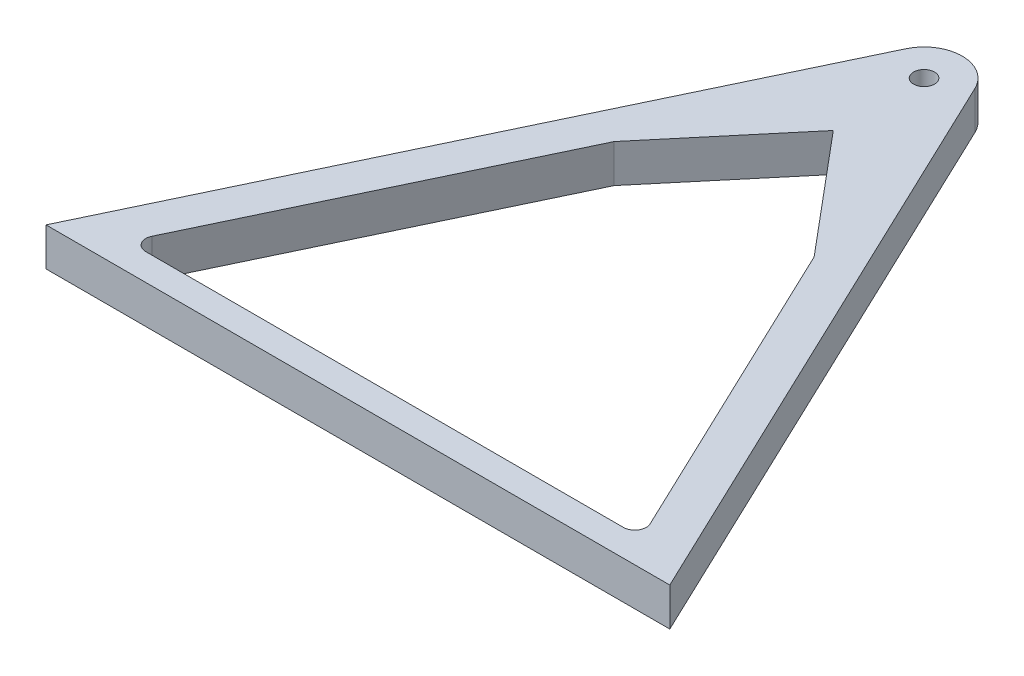
SolidWorks part; units mm, degrees
ref_plane "Front Plane" through (0, 0, 0) normal (0, 0, 1) x (1, 0, 0)
ref_plane "Top Plane" through (0, 0, 0) normal (0, 1, 0) x (1, 0, 0)
ref_plane "Right Plane" through (0, 0, 0) normal (1, 0, 0) x (0, 0, -1)
sketch "Sketch1" plane through (0, 0, 0) normal (0, 1, 0) x (1, 0, 0)
  line L0 (76.2, 0) -> (-76.2, 0) construction
  line L1 (0, 0) -> (0, 160) construction
  line L2 (0, 160) -> (-76.2, 0) construction
  line L3 (-81.7381, 0) -> (0, 171.6285)
  line L4 (0, 148.3715) -> (-67.3282, 7)
  line L5 (-67.3282, 7) -> (67.3282, 7)
  line L6 (0, 160) -> (76.2, 0) construction
  line L7 (67.3282, 7) -> (0, 148.3715)
  line L8 (0, 171.6285) -> (81.7381, 0)
  line L9 (81.7381, 0) -> (-81.7381, 0)
  point P4 (0, 0)
  dimension "D3" = 10
  dimension "D1" = 160
  dimension "D2" = 152.4
  dimension "D5" = 7
extrude "Boss-Extrude1" add sketch "Sketch1" along normal blind 10
fillet "Fillet1" radius 10 1 edges at (0, 5, -171.6285)
fillet "Fillet2" radius 3 3 edges at (67.3282, 5, -7) (-67.3282, 5, -7) (0, 5, -148.3715)
sketch "Sketch5" plane through (0, 10, 0) normal (0, 1, 0) x (1, 0, 0)
  arc A0 (9.0284, 152.6713) -> (-9.0284, 152.6713) centre (0, 148.3715) ccw construction
  circle A1 centre (0, 148.3715) radius 10
extrude "Boss-Extrude2" add sketch "Sketch5" against normal through all
sketch "Sketch4" plane through (0, 10, 0) normal (0, 1, 0) x (1, 0, 0)
  circle A0 centre (0, 148.3715) radius 2.75
  dimension "D1" = 5.5
extrude "Cut-Extrude1" cut sketch "Sketch4" against normal blind 10
sketch "Sketch6" plane through (0, 10, 0) normal (0, 1, 0) x (1, 0, 0)
  line L0 (-26.1937, 93.3715) -> (0, 124.588)
  line L1 (0, 124.588) -> (26.1938, 93.3715)
  line L2 (0, 0) -> (0, 124.588) construction
  line L3 (-4.2998, 139.3431) -> (-65.2851, 11.2899)
  line L4 (65.2851, 11.2899) -> (4.2998, 139.3431)
  line L5 (-62.5766, 7) -> (62.5766, 7)
  line L6 (-4.2998, 139.3431) -> (-26.1937, 93.3715)
  line L7 (26.1938, 93.3715) -> (4.2998, 139.3431)
  arc A3 (-4.2998, 139.3431) -> (4.2998, 139.3431) centre (0, 148.3715) ccw
  arc A4 (62.5766, 7) -> (65.2851, 11.2899) centre (62.5766, 10) ccw
  arc A5 (-65.2851, 11.2899) -> (-62.5766, 7) centre (-62.5766, 10) ccw
  arc A6 (-4.2998, 139.3431) -> (4.2998, 139.3431) centre (0, 148.3715) ccw
  dimension "D2" = 80
  dimension "D3" = 55
  dimension "D1" = 0
extrude "Boss-Extrude3" add sketch "Sketch6" against normal through all
